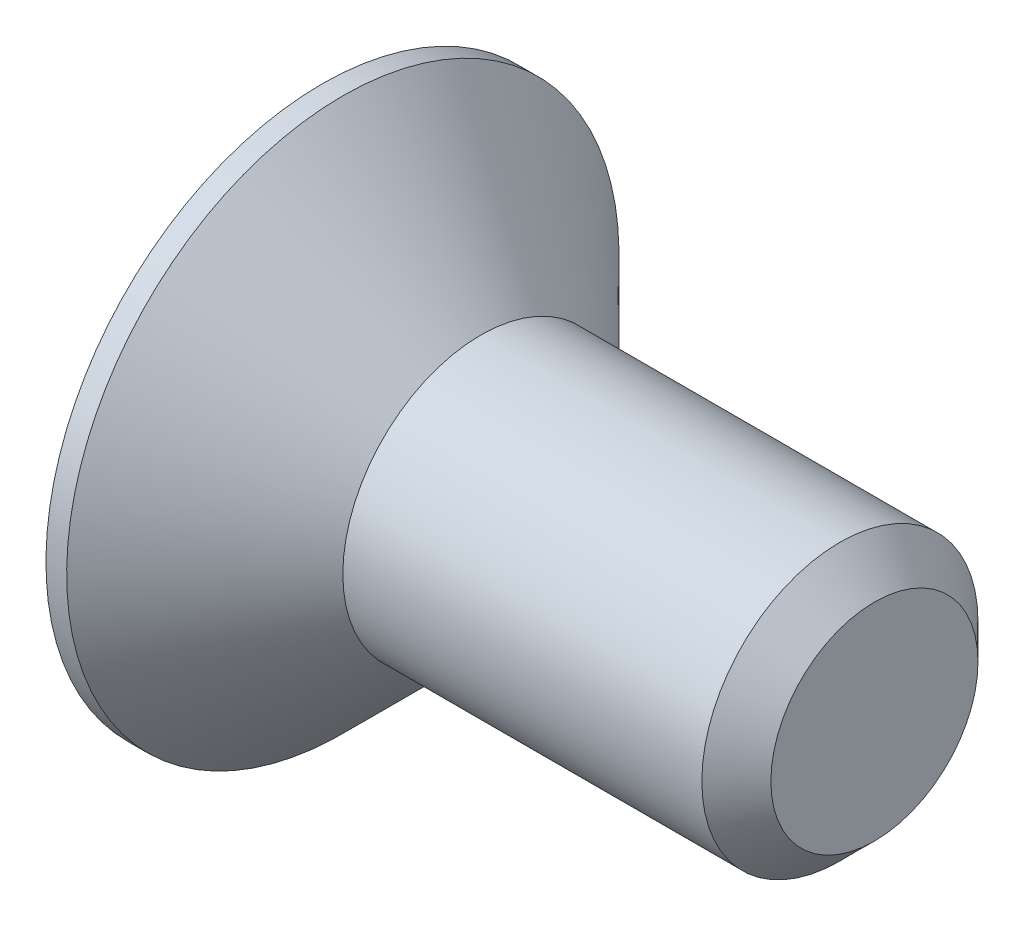
SolidWorks part; units mm, degrees
ref_plane "Plan de face" through (0, 0, 0) normal (0, 0, 1) x (1, 0, 0)
ref_plane "Plan de dessus" through (0, 0, 0) normal (0, 1, 0) x (1, 0, 0)
ref_plane "Plan de droite" through (0, 0, 0) normal (1, 0, 0) x (0, 0, -1)
sketch "Esquisse1" plane through (0, 0, 0) normal (0, 0, 1) x (1, 0, 0)
  line L0 (0, 0) -> (0, 4)
  line L1 (0, 4) -> (0.3, 4)
  line L2 (0.3, 4) -> (2.3, 2)
  line L3 (2.3, 2) -> (8, 2)
  line L4 (8, 2) -> (8, 0)
  line L5 (8, 0) -> (0, 0) construction
  line L6 (0, 0) -> (8, 0)
  dimension "D1" = 2.3
  dimension "D2" = 8
  dimension "D3" = 4
  dimension "D4" = 8
  dimension "D5" = 45
revolve "Révolution1" add sketch "Esquisse1" angle 360 about L5
chamfer "Chanfrein1" distance 0.5 angle 45 1 edges at (8, 2, 0)
sketch "Esquisse2" plane through (0, 0, 0) normal (-1, 0, 0) x (0, 0, 1)
  line L1 (0, 1.4434) -> (-1.25, 0.7217)
  line L2 (-1.25, 0.7217) -> (-1.25, -0.7217)
  line L3 (-1.25, -0.7217) -> (0, -1.4434)
  line L4 (0, -1.4434) -> (1.25, -0.7217)
  line L5 (1.25, -0.7217) -> (1.25, 0.7217)
  line L6 (1.25, 0.7217) -> (0, 1.4434)
  circle A0 centre (0, 0) radius 1.25 construction
  dimension "D1" = 2.5
extrude "Enlèv. mat.-Extru.1" cut sketch "Esquisse2" against normal blind 1.8
